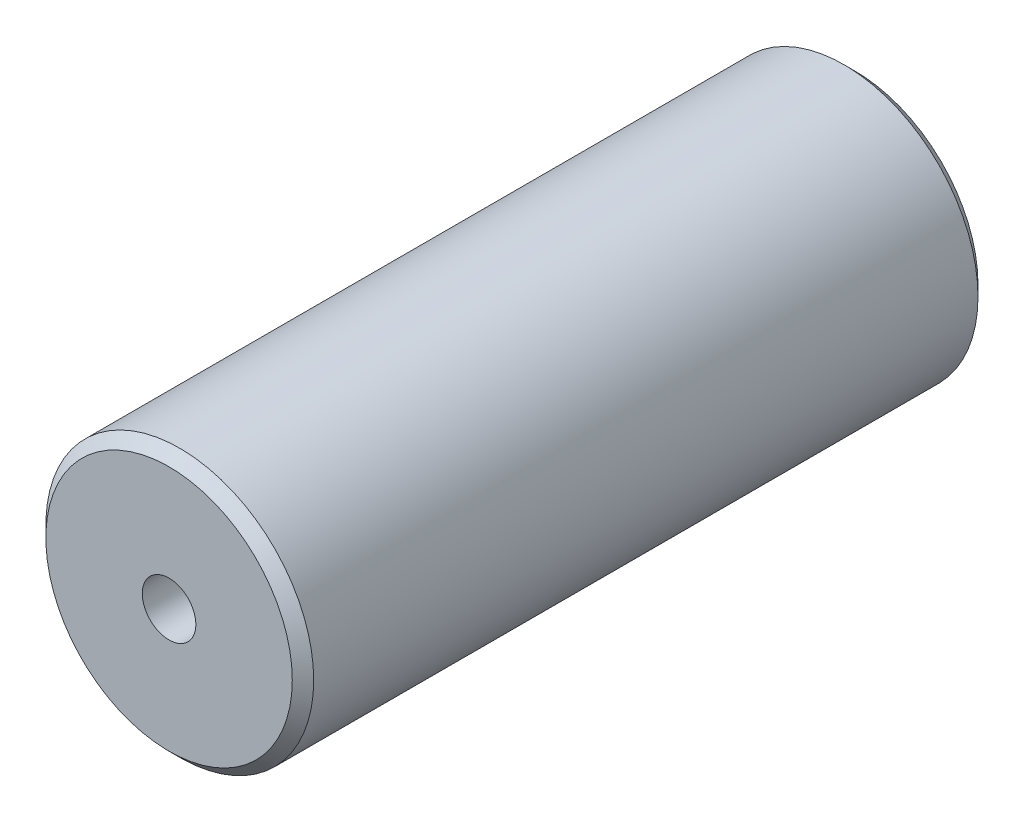
SolidWorks part; units mm, degrees
material "1.0545 (S355N)"
ref_plane "Front Plane" through (0, 0, 0) normal (0, 0, 1) x (1, 0, 0)
ref_plane "Top Plane" through (0, 0, 0) normal (0, 1, 0) x (1, 0, 0)
ref_plane "Right Plane" through (0, 0, 0) normal (1, 0, 0) x (0, 0, -1)
sketch "Sketch1" plane through (0, 0, 0) normal (0, 0, 1) x (1, 0, 0)
  circle A0 centre (0, 0) radius 12.5
  dimension "D1" = 25
extrude "Boss-Extrude1" add sketch "Sketch1" along normal mid plane 64
chamfer "Chamfer1" distance 1 angle 45 2 edges at (12.5, 0, -32) (12.5, 0, 32)
hole_wizard "M6 Tapped Hole1" positions "Sketch2" profile "Sketch4" tap size "M6" standard "ISO"
sketch "Sketch2" plane through (0, 0, 32) normal (0, 0, 1) x (1, 0, 0)
  point P0 (0, 0)
sketch "Sketch4" plane through (0, 0, 32) normal (1, 0, 0) x (0, -1, 0)
  line L0 (0, 0) -> (0, 16.5022)
  line L1 (0, 16.5022) -> (2.5, 15)
  line L2 (2.5, 15) -> (2.5, 0)
  line L5 (2.5, 0) -> (0, 0)
  line L10 (0, 16.5022) -> (-2.5, 15) construction
  line L11 (0, -6.35) -> (0, 107.95) construction
  dimension "Tap Drill Dia." = 5
  dimension "Tap Drill Depth" = 15
  dimension "Drill Angle" = 118
cosmetic thread "Hole Thread1"
mirror "Mirror1" about plane through (0, 0, 0) normal (0, 0, 1) of "M6 Tapped Hole1"
cosmetic thread "Hole Thread2" parameters "D1"=12, "D2"=6
